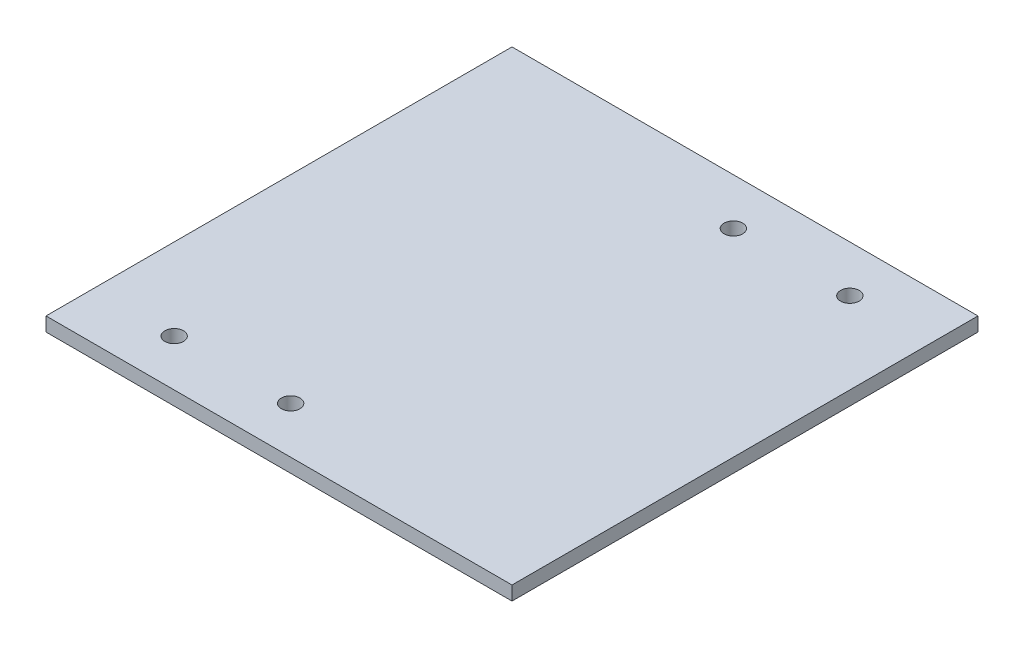
SolidWorks part; units mm, degrees
ref_plane "Plan de face" through (0, 0, 0) normal (0, 0, 1) x (1, 0, 0)
ref_plane "Plan de dessus" through (0, 0, 0) normal (0, 1, 0) x (1, 0, 0)
ref_plane "Plan de droite" through (0, 0, 0) normal (1, 0, 0) x (0, 0, -1)
sketch "Esquisse1" plane through (0, 0, 0) normal (0, 1, 0) x (1, 0, 0)
  line L0 (-50, 0) -> (50, 0) construction
  line L1 (-50, -50) -> (50, -50)
  line L2 (-50, -50) -> (-50, 50)
  line L3 (-50, 50) -> (50, 50)
  line L4 (50, -50) -> (50, 50)
  line L5 (-50, -50) -> (50, 50) construction
  line L6 (-50, 50) -> (50, -50) construction
  line L8 (0, 50) -> (0, -50) construction
  circle A0 centre (-32.5, -40) radius 2
  circle A1 centre (-7.5, -40) radius 2
  circle A2 centre (7.5, 40) radius 2
  circle A3 centre (32.5, 40) radius 2
  point P0 (0, 0)
  dimension "D3" = 4
  dimension "D6" = 4
  dimension "D7" = 25
  dimension "D9" = 4
  dimension "D10" = 4
  dimension "D13" = 40
  dimension "D14" = 40
  dimension "D5" = 40
  dimension "D8" = 40
  dimension "D4" = 7.5
  dimension "D1" = 100
  dimension "D2" = 100
  dimension "D11" = 25
  dimension "D12" = 7.5
extrude "Boss.-Extru.1" add sketch "Esquisse1" along normal blind 3
